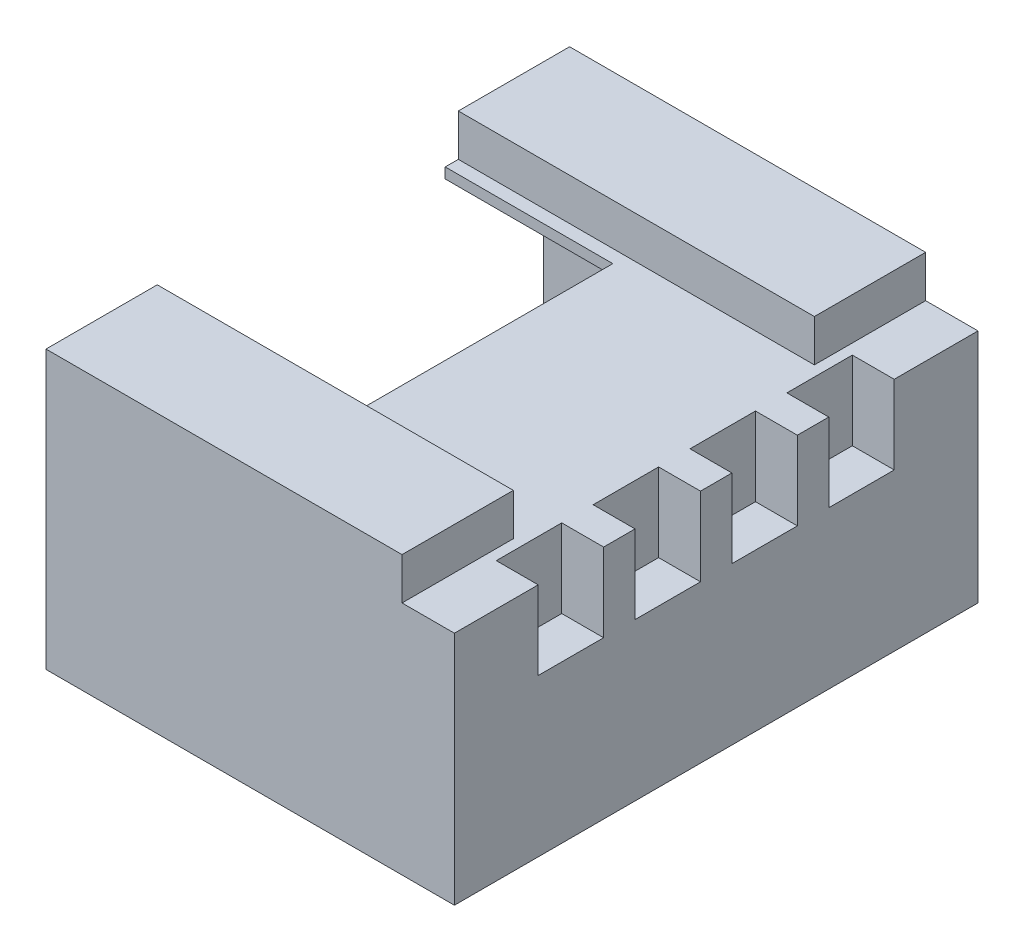
SolidWorks part; units mm, degrees
ref_plane "Plan de face" through (0, 0, 0) normal (0, 0, 1) x (1, 0, 0)
ref_plane "Plan de dessus" through (0, 0, 0) normal (0, 1, 0) x (1, 0, 0)
ref_plane "Plan de droite" through (0, 0, 0) normal (1, 0, 0) x (0, 0, -1)
ref_plane "Plan2" through (0, 0, -3.6) normal (0, 0, -1) x (-1, 0, 0)
sketch "Esquisse7" plane through (0, 0, -3.6) normal (0, 0, -1) x (-1, 0, 0)
  line L0 (-7.55, 3.1) -> (-3.55, 3.1)
  line L1 (-3.55, 3.1) -> (-3.55, 3.4)
  line L2 (-3.55, 3.4) -> (-7.55, 3.4)
  line L3 (-7.55, 3.4) -> (-7.55, 3.1)
  dimension "D1" = 4
  dimension "D2" = 0.3
  dimension "D3" = 3.1
  dimension "D4" = 3.55
extrude "Boss.-Extru.2" add sketch "Esquisse7" against normal blind 0.3 separate body
ref_plane "Plan3" through (0, 6.05, 0) normal (0, 1, 0) x (1, 0, 0)
sketch "Esquisse12" plane through (0, 6.05, 0) normal (0, 1, 0) x (1, 0, 0)
  line L0 (1.45, 5) -> (1.45, -5)
  line L1 (1.45, -5) -> (9.25, -5)
  line L2 (9.25, -5) -> (9.25, 5)
  line L3 (9.25, 5) -> (1.45, 5)
  line L4 (-0.8887, 0) -> (10.5397, 0) construction
  dimension "D1" = 10
extrude "Boss.-Extru.3" add sketch "Esquisse12" against normal blind 5.3 separate body
sketch "Esquisse13" plane through (1.45, 0, 0) normal (-1, 0, 0) x (0, 0, 1)
  line L0 (-4.5, 5.55) -> (-4.5, 1.25)
  line L1 (-4.5, 1.25) -> (4.5, 1.25)
  line L2 (4.5, 1.25) -> (4.5, 5.55)
  line L3 (4.5, 5.55) -> (3.5, 5.55)
  line L4 (3.5, 5.55) -> (3.5, 5.05)
  line L5 (3.5, 5.05) -> (-3.5, 5.05)
  line L6 (-3.5, 5.05) -> (-3.5, 5.55)
  line L7 (-3.5, 5.55) -> (-4.5, 5.55)
  line L8 (0, -0.6971) -> (0, 6.7234) construction
  line L9 (-5, 0.75) -> (5, 0.75) construction
  line L10 (-5, 6.05) -> (5, 6.05) construction
  point P11 (-3.5, 5.3)
  point P12 (3.5, 5.3)
  dimension "D1" = 9
  dimension "D2" = 7
  dimension "D3" = 0.5
  dimension "D4" = 0.5
  dimension "D5" = 0.5
extrude "Enlèv. mat.-Extru.3" cut sketch "Esquisse13" against normal blind 6.1
sketch "Esquisse14" plane through (0, 6.05, 0) normal (0, 1, 0) x (-1, 0, 0)
  line L0 (-1.45, 2.625) -> (-4.65, 2.625)
  line L1 (-4.65, 2.625) -> (-4.65, -2.625)
  line L2 (-4.65, -2.625) -> (-1.45, -2.625)
  line L3 (-1.45, -2.625) -> (-1.45, 2.625)
  line L4 (1.0836, 0) -> (-10.1804, 0) construction
  line L5 (-1.45, -5) -> (-1.45, 5) construction
  dimension "D1" = 3.2
  dimension "D2" = 5.25
extrude "Enlèv. mat.-Extru.4" cut sketch "Esquisse14" against normal up to next (1 mm away)
pattern_linear "Répétition linéaire1" count 4 spacing 2.3 along (0, 0, 1) of "Boss.-Extru.2"
sketch "Esquisse15" plane through (0, 6.05, 0) normal (0, 1, 0) x (1, 0, 0)
  line L0 (-1.4029, 0) -> (6.993, 0) construction
  line L1 (4.65, -2.625) -> (4.65, 2.625) construction
  line L2 (1.2527, 2.875) -> (4.65, 2.875)
  line L3 (1.2527, 2.875) -> (1.2527, -2.875)
  line L4 (1.2527, -2.875) -> (4.65, -2.875)
  line L5 (4.65, 2.875) -> (4.65, -2.875)
  line L6 (4.65, 2.625) -> (1.45, 2.625) construction
  dimension "D1" = 0.25
extrude "Enlèv. mat.-Extru.5" cut sketch "Esquisse15" against normal blind 0.8
sketch "Esquisse16" plane through (0, 6.05, 0) normal (0, 1, 0) x (1, 0, 0)
  line L0 (-1.2358, 0) -> (9.9169, 0) construction
  line L1 (1.45, -2.875) -> (4.65, -2.875) construction
  line L2 (1.45, 2.875) -> (10.9611, 2.875)
  line L3 (1.45, 2.875) -> (1.45, -2.875)
  line L4 (1.45, -2.875) -> (10.9611, -2.875)
  line L5 (10.9611, 2.875) -> (10.9611, -2.875)
extrude "Enlèv. mat.-Extru.6" cut sketch "Esquisse16" against normal blind 0.8
sketch "Esquisse17" plane through (0, 6.05, 0) normal (0, 1, 0) x (1, 0, 0)
  line L0 (9.25, 2.875) -> (9.25, 5) construction
  line L1 (8.25, 5.3466) -> (10.3273, 5.3466)
  line L2 (8.25, 5.3466) -> (8.25, -5.3327)
  line L3 (8.25, -5.3327) -> (10.3273, -5.3327)
  line L4 (10.3273, 5.3466) -> (10.3273, -5.3327)
  dimension "D1" = 1
extrude "Enlèv. mat.-Extru.7" cut sketch "Esquisse17" against normal up to surface (0.8 mm away) up to face at (4.2, 5.25, 0)
sketch "Esquisse18" plane through (0, 5.25, 0) normal (0, 1, 0) x (1, 0, 0)
  line L0 (-0.868, 0) -> (10.4248, 0) construction
  line L1 (9.25, 5) -> (9.25, -5) construction
  line L2 (8.45, 1.55) -> (9.75, 1.55)
  line L3 (8.45, 1.55) -> (8.45, 0.3)
  line L4 (8.45, 0.3) -> (9.75, 0.3)
  line L5 (9.75, 1.55) -> (9.75, 0.3)
  line L6 (8.45, 3.4) -> (9.75, 3.4)
  line L7 (8.45, 3.4) -> (8.45, 2.15)
  line L8 (8.45, 2.15) -> (9.75, 2.15)
  line L9 (9.75, 3.4) -> (9.75, 2.15)
  line L10 (9.75, -3.4) -> (9.75, -2.15)
  line L11 (8.45, -3.4) -> (9.75, -3.4)
  line L12 (8.45, -3.4) -> (8.45, -2.15)
  line L13 (8.45, -2.15) -> (9.75, -2.15)
  line L14 (9.75, -1.55) -> (9.75, -0.3)
  line L15 (8.45, -1.55) -> (9.75, -1.55)
  line L16 (8.45, -0.3) -> (9.75, -0.3)
  line L17 (8.45, -1.55) -> (8.45, -0.3)
  point P11 (8.45, 2.775)
  point P14 (9.75, 0.925)
  point P15 (9.75, 2.775)
  dimension "D1" = 1.25
  dimension "D2" = 1.25
  dimension "D3" = 0.3
  dimension "D4" = 0.6
  dimension "D5" = 0.8
  dimension "D6" = 1.3
extrude "Enlèv. mat.-Extru.8" cut sketch "Esquisse18" against normal blind 1.5
